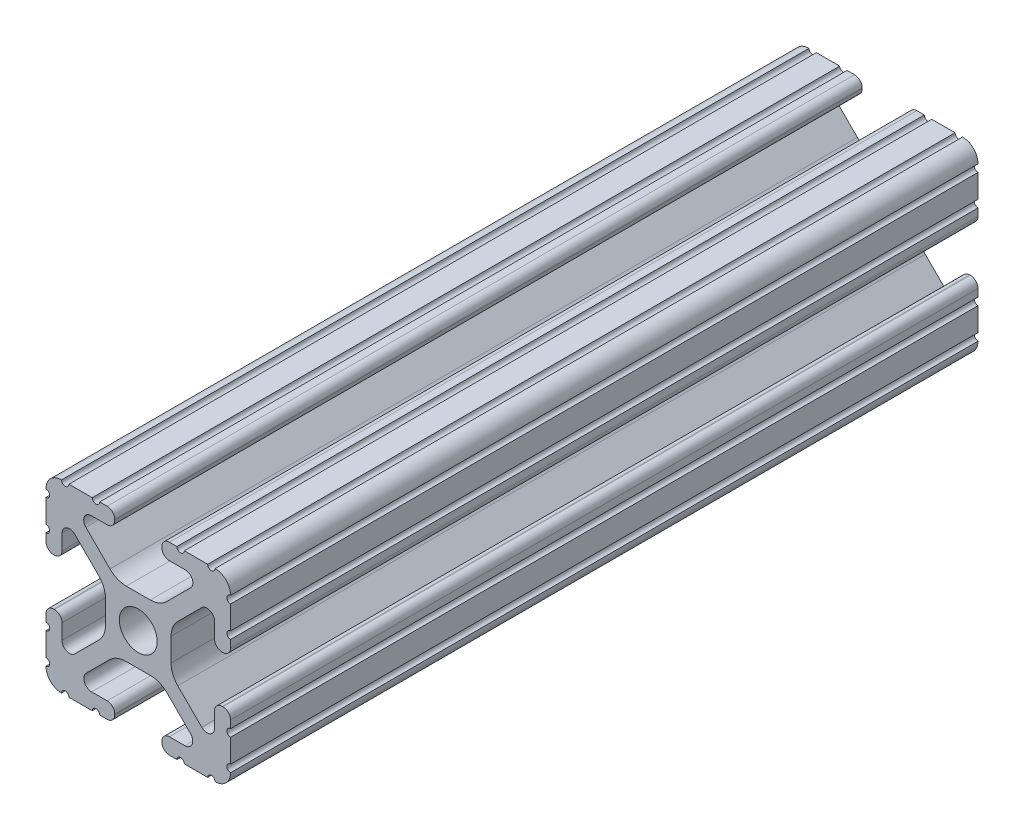
SolidWorks part; units mm, degrees
material "6105-T5"
ref_plane "Front Plane" through (0, 0, 0) normal (0, 0, 1) x (1, 0, 0)
ref_plane "Top Plane" through (0, 0, 0) normal (0, 1, 0) x (1, 0, 0)
ref_plane "Right Plane" through (0, 0, 0) normal (1, 0, 0) x (0, 0, -1)
sketch "Sketch1" plane through (0, 0, 0) normal (0, 0, 1) x (1, 0, 0)
  line L1 (12.7, 12.7) -> (-12.7, 12.7) construction
  line L2 (12.7, 12.7) -> (12.7, -12.7) construction
  line L3 (12.7, -12.7) -> (-12.7, -12.7) construction
  line L4 (-12.7, 12.7) -> (-12.7, -12.7) construction
  line L5 (12.7, 12.7) -> (-12.7, -12.7) construction
  line L6 (12.7, -12.7) -> (-12.7, 12.7) construction
  line L88 (-1.7093, -4.4958) -> (1.7093, -4.4958)
  line L89 (3.9523, -5.4237) -> (7.1797, -8.6452)
  line L90 (6.4164, -10.4902) -> (4.2875, -10.4902)
  line L91 (3.2385, -11.5392) -> (3.2385, -11.651)
  line L92 (4.2875, -12.7) -> (5.3171, -12.7)
  line L93 (6.3331, -12.7) -> (9.5504, -12.7)
  line L94 (12.7, -9.5504) -> (12.7, -6.3331)
  line L95 (12.7, -5.3171) -> (12.7, -4.2875)
  line L96 (11.651, -3.2385) -> (11.5392, -3.2385)
  line L97 (10.4902, -4.2875) -> (10.4902, -6.4021)
  line L98 (8.737, -7.1292) -> (5.4405, -3.8388)
  line L99 (4.5085, -1.5917) -> (4.5085, 1.5917)
  line L100 (5.4405, 3.8388) -> (8.737, 7.1292)
  line L101 (10.4902, 6.4021) -> (10.4902, 4.2875)
  line L102 (11.5392, 3.2385) -> (11.651, 3.2385)
  line L103 (12.7, 4.2875) -> (12.7, 5.3171)
  line L104 (12.7, 6.3331) -> (12.7, 9.5504)
  line L105 (9.5504, 12.7) -> (6.3331, 12.7)
  line L106 (5.3171, 12.7) -> (4.2875, 12.7)
  line L107 (3.2384, 11.651) -> (3.2384, 11.5392)
  line L108 (4.2875, 10.4902) -> (6.4768, 10.4902)
  line L109 (7.2072, 8.7245) -> (3.9003, 5.4237)
  line L110 (1.6573, 4.4958) -> (-1.6573, 4.4958)
  line L111 (-3.9003, 5.4237) -> (-7.2072, 8.7245)
  line L112 (-6.4768, 10.4902) -> (-4.2875, 10.4902)
  line L113 (-3.2384, 11.5392) -> (-3.2384, 11.651)
  line L114 (-4.2875, 12.7) -> (-5.3171, 12.7)
  line L115 (-6.3331, 12.7) -> (-9.5504, 12.7)
  line L116 (-12.7, 9.5504) -> (-12.7, 6.3331)
  line L117 (-12.7, 5.3171) -> (-12.7, 4.2875)
  line L118 (-11.651, 3.2385) -> (-11.5392, 3.2385)
  line L119 (-10.4902, 4.2875) -> (-10.4902, 6.4021)
  line L120 (-8.737, 7.1292) -> (-5.4405, 3.8388)
  line L121 (-4.5085, 1.5917) -> (-4.5085, -1.5917)
  line L122 (-5.4405, -3.8388) -> (-8.737, -7.1292)
  line L123 (-10.4902, -6.4021) -> (-10.4902, -4.2875)
  line L124 (-11.5392, -3.2385) -> (-11.651, -3.2385)
  line L125 (-12.7, -4.2875) -> (-12.7, -5.3171)
  line L126 (-12.7, -6.3331) -> (-12.7, -9.5504)
  line L127 (-9.5504, -12.7) -> (-6.3331, -12.7)
  line L128 (-5.3171, -12.7) -> (-4.2875, -12.7)
  line L129 (-3.2385, -11.651) -> (-3.2385, -11.5392)
  line L130 (-4.2875, -10.4902) -> (-6.4164, -10.4902)
  line L131 (-7.1797, -8.6452) -> (-3.9523, -5.4237)
  circle A1 centre (0, 0) radius 2.6035
  arc A104 (-1.7093, -4.4958) -> (-3.9523, -5.4237) centre (-1.7093, -7.6708) ccw
  arc A105 (3.9523, -5.4237) -> (1.7093, -4.4958) centre (1.7093, -7.6708) ccw
  arc A106 (6.4164, -10.4902) -> (7.1797, -8.6452) centre (6.4164, -9.4098) ccw
  arc A107 (4.2875, -10.4902) -> (3.2385, -11.5392) centre (4.2875, -11.5392) ccw
  arc A108 (3.2385, -11.651) -> (4.2875, -12.7) centre (4.2875, -11.651) ccw
  arc A109 (6.3331, -12.7) -> (5.3171, -12.7) centre (5.8251, -12.7) ccw
  arc A110 (10.5664, -12.6998) -> (9.5504, -12.7) centre (10.0584, -12.7) ccw
  arc A111 (10.5664, -12.6998) -> (12.6998, -10.5664) centre (10.5918, -10.5918) ccw
  arc A112 (12.7, -9.5504) -> (12.6998, -10.5664) centre (12.7, -10.0584) ccw
  arc A113 (12.7, -5.3171) -> (12.7, -6.3331) centre (12.7, -5.8251) ccw
  arc A114 (12.7, -4.2875) -> (11.651, -3.2385) centre (11.651, -4.2875) ccw
  arc A115 (11.5392, -3.2385) -> (10.4902, -4.2875) centre (11.5392, -4.2875) ccw
  arc A116 (8.737, -7.1292) -> (10.4902, -6.4021) centre (9.4628, -6.4021) ccw
  arc A117 (4.5085, -1.5917) -> (5.4405, -3.8388) centre (7.6835, -1.5917) ccw
  arc A118 (5.4405, 3.8388) -> (4.5085, 1.5917) centre (7.6835, 1.5917) ccw
  arc A119 (10.4902, 6.4021) -> (8.737, 7.1292) centre (9.4628, 6.4021) ccw
  arc A120 (10.4902, 4.2875) -> (11.5392, 3.2385) centre (11.5392, 4.2875) ccw
  arc A121 (11.651, 3.2385) -> (12.7, 4.2875) centre (11.651, 4.2875) ccw
  arc A122 (12.7, 6.3331) -> (12.7, 5.3171) centre (12.7, 5.8251) ccw
  arc A123 (12.6998, 10.5664) -> (12.7, 9.5504) centre (12.7, 10.0584) ccw
  arc A124 (12.6998, 10.5664) -> (10.5664, 12.6998) centre (10.5918, 10.5918) ccw
  arc A125 (9.5504, 12.7) -> (10.5664, 12.6998) centre (10.0584, 12.7) ccw
  arc A126 (5.3171, 12.7) -> (6.3331, 12.7) centre (5.8251, 12.7) ccw
  arc A127 (4.2875, 12.7) -> (3.2384, 11.651) centre (4.2875, 11.651) ccw
  arc A128 (3.2384, 11.5392) -> (4.2875, 10.4902) centre (4.2875, 11.5392) ccw
  arc A129 (7.2072, 8.7245) -> (6.4768, 10.4902) centre (6.4768, 9.4563) ccw
  arc A130 (1.6573, 4.4958) -> (3.9003, 5.4237) centre (1.6573, 7.6708) ccw
  arc A131 (-3.9003, 5.4237) -> (-1.6573, 4.4958) centre (-1.6573, 7.6708) ccw
  arc A132 (-6.4768, 10.4902) -> (-7.2072, 8.7245) centre (-6.4768, 9.4563) ccw
  arc A133 (-4.2875, 10.4902) -> (-3.2384, 11.5392) centre (-4.2875, 11.5392) ccw
  arc A134 (-3.2384, 11.651) -> (-4.2875, 12.7) centre (-4.2875, 11.651) ccw
  arc A135 (-6.3331, 12.7) -> (-5.3171, 12.7) centre (-5.8251, 12.7) ccw
  arc A136 (-10.5664, 12.6998) -> (-9.5504, 12.7) centre (-10.0584, 12.7) ccw
  arc A137 (-10.5664, 12.6998) -> (-12.6998, 10.5664) centre (-10.5918, 10.5918) ccw
  arc A138 (-12.7, 9.5504) -> (-12.6998, 10.5664) centre (-12.7, 10.0584) ccw
  arc A139 (-12.7, 5.3171) -> (-12.7, 6.3331) centre (-12.7, 5.8251) ccw
  arc A140 (-12.7, 4.2875) -> (-11.651, 3.2385) centre (-11.651, 4.2875) ccw
  arc A141 (-11.5392, 3.2385) -> (-10.4902, 4.2875) centre (-11.5392, 4.2875) ccw
  arc A142 (-8.737, 7.1292) -> (-10.4902, 6.4021) centre (-9.4628, 6.4021) ccw
  arc A143 (-4.5085, 1.5917) -> (-5.4405, 3.8388) centre (-7.6835, 1.5917) ccw
  arc A144 (-5.4405, -3.8388) -> (-4.5085, -1.5917) centre (-7.6835, -1.5917) ccw
  arc A145 (-10.4902, -6.4021) -> (-8.737, -7.1292) centre (-9.4628, -6.4021) ccw
  arc A146 (-10.4902, -4.2875) -> (-11.5392, -3.2385) centre (-11.5392, -4.2875) ccw
  arc A147 (-11.651, -3.2385) -> (-12.7, -4.2875) centre (-11.651, -4.2875) ccw
  arc A148 (-12.7, -6.3331) -> (-12.7, -5.3171) centre (-12.7, -5.8251) ccw
  arc A149 (-12.6998, -10.5664) -> (-12.7, -9.5504) centre (-12.7, -10.0584) ccw
  arc A150 (-12.6998, -10.5664) -> (-10.5664, -12.6998) centre (-10.5918, -10.5918) ccw
  arc A151 (-9.5504, -12.7) -> (-10.5664, -12.6998) centre (-10.0584, -12.7) ccw
  arc A152 (-5.3171, -12.7) -> (-6.3331, -12.7) centre (-5.8251, -12.7) ccw
  arc A153 (-4.2875, -12.7) -> (-3.2385, -11.651) centre (-4.2875, -11.651) ccw
  arc A154 (-3.2385, -11.5392) -> (-4.2875, -10.4902) centre (-4.2875, -11.5392) ccw
  arc A155 (-7.1797, -8.6452) -> (-6.4164, -10.4902) centre (-6.4164, -9.4098) ccw
  point P3 (0, 0)
  point P21 (-12.7, 0)
  point P22 (0, 12.7)
  point P25 (12.7, 0)
  point P28 (0, -12.7)
  point P30 (-12.7, -12.7)
  point P33 (12.7, -12.7)
  point P37 (12.7, 12.7)
  point P40 (-12.7, 12.7)
  dimension "D1" = 25.4
extrude "Extrude1" add sketch "Sketch1" against normal blind 102.87
